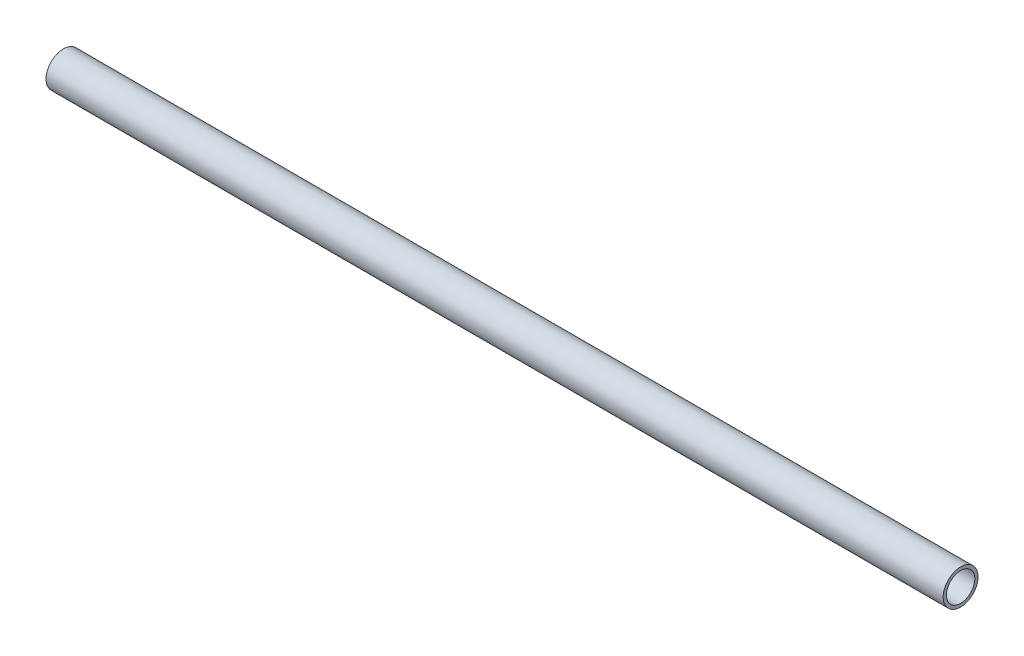
SolidWorks part; units mm, degrees
ref_plane "Front Plane" through (0, 0, 0) normal (0, 0, 1) x (1, 0, 0)
ref_plane "Top Plane" through (0, 0, 0) normal (0, 1, 0) x (1, 0, 0)
ref_plane "Right Plane" through (0, 0, 0) normal (1, 0, 0) x (0, 0, -1)
sketch "Sketch1" plane through (0, 0, 0) normal (0, 0, 1) x (1, 0, 0)
  line L1 (0, 0) -> (496.9305, 0) construction
  line L2 (0, 0) -> (0, 7.874) construction
  line L3 (0, 7.874) -> (496.9305, 7.874)
  line L4 (496.9305, 0) -> (496.9305, 7.874) construction
  line L5 (0, 7.874) -> (496.9305, 7.874) construction
  line L6 (0, 7.874) -> (0, 9.652)
  line L7 (0, 9.652) -> (496.9305, 9.652)
  line L8 (496.9305, 7.874) -> (496.9305, 9.652)
  dimension "D1" = 9.652
  dimension "D2" = 1.778
  dimension "D3" = 496.9305
revolve "Revolve1" add sketch "Sketch1" angle 360 about L1
